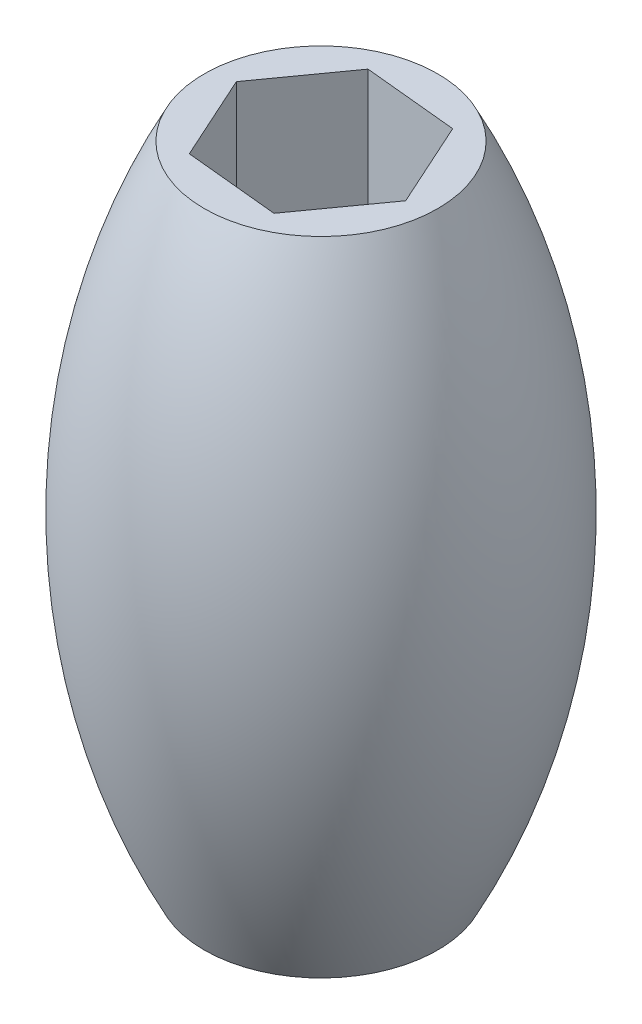
SolidWorks part; units mm, degrees
ref_plane "Front Plane" through (0, 0, 0) normal (0, 0, 1) x (1, 0, 0)
ref_plane "Top Plane" through (0, 0, 0) normal (0, 1, 0) x (1, 0, 0)
ref_plane "Right Plane" through (0, 0, 0) normal (1, 0, 0) x (0, 0, -1)
sketch "Sketch1" plane through (0, 0, 0) normal (0, 1, 0) x (1, 0, 0)
  circle A0 centre (0, 0) radius 19.05
extrude "Boss-Extrude1" add sketch "Sketch1" along normal blind 104.775
sketch "Sketch2" plane through (0, 0, 0) normal (0, -1, 0) x (1, 0, 0)
  line L1 (-15.3236, -1.5108) -> (-6.3534, -14.026)
  line L2 (-6.3534, -14.026) -> (8.9702, -12.5153)
  line L3 (8.9702, -12.5153) -> (15.3236, 1.5108)
  line L4 (15.3236, 1.5108) -> (6.3534, 14.026)
  line L5 (6.3534, 14.026) -> (-8.9702, 12.5153)
  line L6 (-8.9702, 12.5153) -> (-15.3236, -1.5108)
  circle A0 centre (0, 0) radius 13.335 construction
extrude "Cut-Extrude1" cut sketch "Sketch2" against normal up to surface (104.775 mm away) up to face at (0, 104.775, 19.05)
sketch "Sketch4" plane through (0, 0, 0) normal (0, 0, 1) x (1, 0, 0)
  line L0 (-19.05, 104.775) -> (-19.05, 0)
  line L1 (0, 0) -> (0, 104.775) construction
  line L2 (19.05, 104.775) -> (-19.05, 104.775) construction
  arc A0 (-19.05, 0) -> (-19.05, 104.775) centre (82.6492, 52.3875) cw
  point P5 (-31.75, 52.3875)
  point P6 (-19.05, 52.3875)
  dimension "D1" = 12.7
revolve "Revolve1" add sketch "Sketch4" angle 360 about L1
